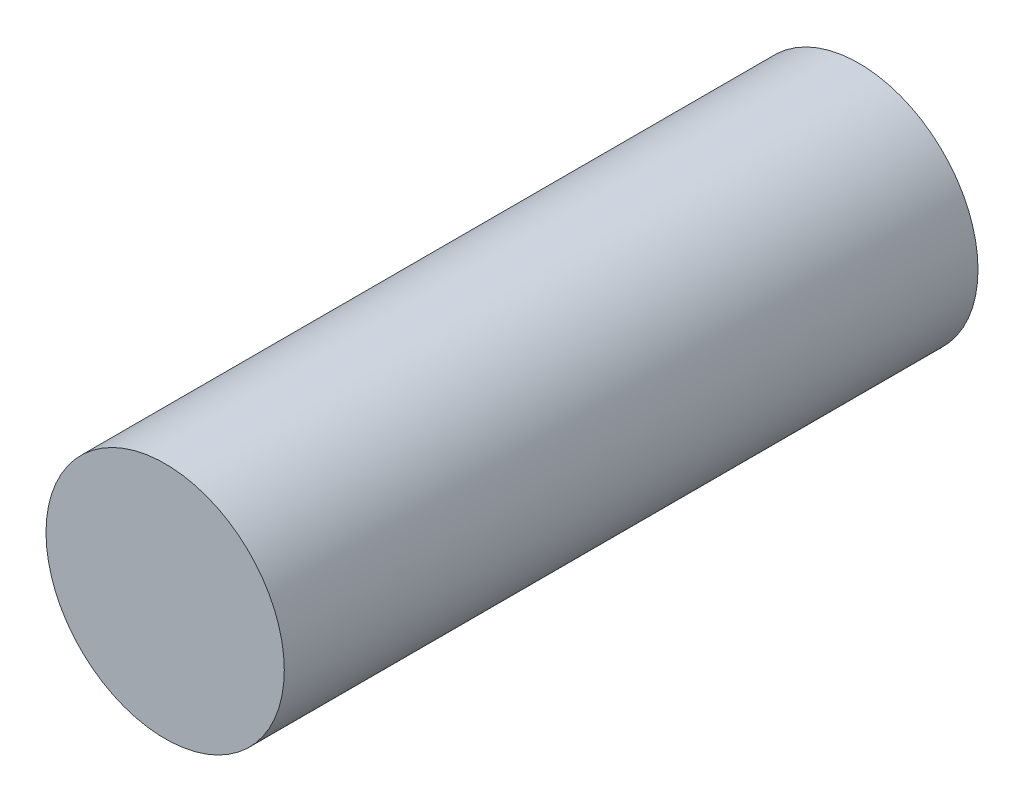
SolidWorks part; units mm, degrees
ref_plane "Front Plane" through (0, 0, 0) normal (0, 0, 1) x (1, 0, 0)
ref_plane "Top Plane" through (0, 0, 0) normal (0, 1, 0) x (1, 0, 0)
ref_plane "Right Plane" through (0, 0, 0) normal (1, 0, 0) x (0, 0, -1)
sketch "Sketch1" plane through (0, 0, 0) normal (0, 0, 1) x (1, 0, 0)
  circle A2 centre (108.0429, 14.6365) radius 4.3625
  circle A3 centre (108.0429, 14.6365) radius 4.3625
  dimension "D1" = 0.4
extrude "Boss-Extrude1" add sketch "Sketch1" against normal up to surface (25.4 mm away)
